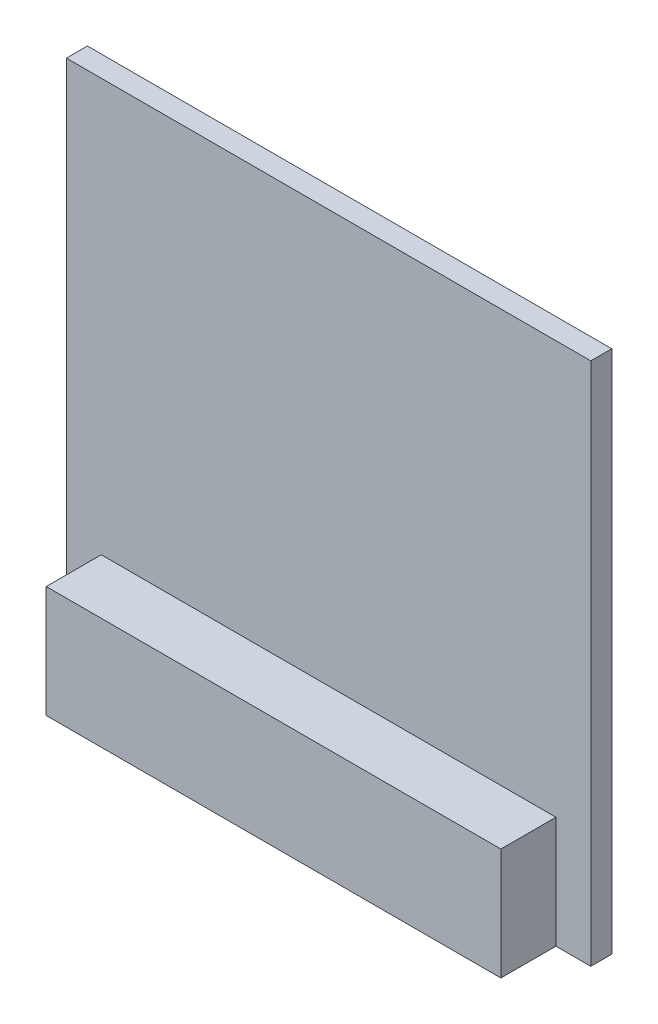
SolidWorks part; units mm, degrees
ref_plane "Front Plane" through (0, 0, 0) normal (0, 0, 1) x (1, 0, 0)
ref_plane "Top Plane" through (0, 0, 0) normal (0, 1, 0) x (1, 0, 0)
ref_plane "Right Plane" through (0, 0, 0) normal (1, 0, 0) x (0, 0, -1)
sketch "Sketch1" plane through (0, 0, 0) normal (0, 0, 1) x (1, 0, 0)
  line L1 (-12.7, -12.7) -> (12.7, -12.7)
  line L2 (-12.7, -12.7) -> (-12.7, 12.7)
  line L3 (-12.7, 12.7) -> (12.7, 12.7)
  line L4 (12.7, -12.7) -> (12.7, 12.7)
  line L5 (-12.7, -12.7) -> (12.7, 12.7) construction
  line L6 (-12.7, 12.7) -> (12.7, -12.7) construction
  point P0 (0, 0)
  dimension "D1" = 25.4
  dimension "D2" = 25.4
extrude "Boss-Extrude1" add sketch "Sketch1" along normal blind 1.016
sketch "Sketch2" plane through (0, 0, 1.016) normal (0, 0, 1) x (1, 0, 0)
  line L0 (-12.7, -12.7) -> (12.7, -12.7) construction
  line L1 (-11.0109, -12.7) -> (11.0109, -12.7)
  line L2 (-11.0109, -12.7) -> (-11.0109, -7.2898)
  line L3 (-11.0109, -7.2898) -> (11.0109, -7.2898)
  line L4 (11.0109, -12.7) -> (11.0109, -7.2898)
  line L5 (-12.7, 12.7) -> (-12.7, -12.7) construction
  dimension "D1" = 22.0218
  dimension "D2" = 5.4102
  dimension "D3" = 1.6891
extrude "Boss-Extrude2" add sketch "Sketch2" along normal blind 2.667
sketch "Sketch3" plane through (0, 0, 0) normal (0, 0, -1) x (-1, 0, 0)
  line L0 (0, 0) -> (0, -12.7) construction
  line L5 (12.7, -12.7) -> (-12.7, -12.7) construction
  line L7 (-4.0132, -7.4676) -> (4.0132, -7.4676)
  line L8 (-4.0132, -7.4676) -> (-4.0132, 0.508)
  line L9 (-4.0132, 0.508) -> (4.0132, 0.508)
  line L10 (4.0132, -7.4676) -> (4.0132, 0.508)
  line L11 (-4.0132, -7.4676) -> (4.0132, 0.508) construction
  line L12 (-4.0132, 0.508) -> (4.0132, -7.4676) construction
  point P0 (0, -3.4798)
  dimension "D1" = 5.2324
  dimension "D2" = 7.9756
  dimension "D3" = 8.0264
extrude "Boss-Extrude3" add sketch "Sketch3" along normal blind 3.589
